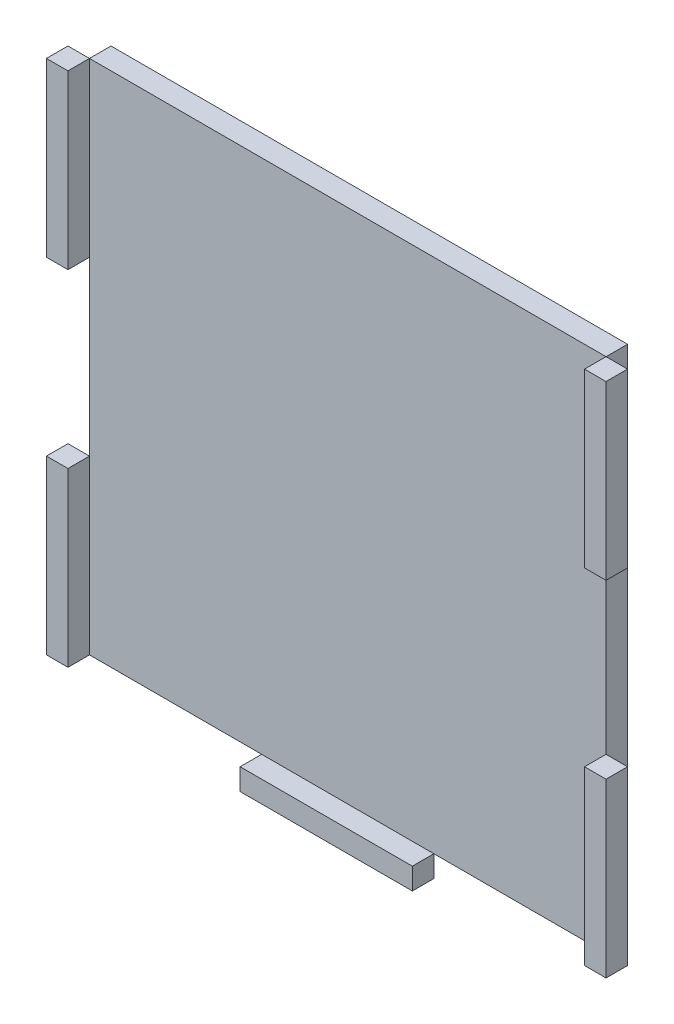
SolidWorks part; units mm, degrees
ref_plane "Front Plane" through (0, 0, 0) normal (0, 0, 1) x (1, 0, 0)
ref_plane "Top Plane" through (0, 0, 0) normal (0, 1, 0) x (1, 0, 0)
ref_plane "Right Plane" through (0, 0, 0) normal (1, 0, 0) x (0, 0, -1)
sketch "Sketch2" plane through (0, 0, 0) normal (0, 0, 1) x (1, 0, 0)
  line L1 (-38.1, -38.1) -> (38.1, -38.1)
  line L2 (-38.1, -38.1) -> (-38.1, 38.1)
  line L3 (-38.1, 38.1) -> (38.1, 38.1)
  line L4 (38.1, -38.1) -> (38.1, 38.1)
  line L5 (-38.1, -38.1) -> (38.1, 38.1) construction
  line L6 (-38.1, 38.1) -> (38.1, -38.1) construction
  point P0 (0, 0)
  dimension "D1" = 76.2
  dimension "D2" = 76.2
extrude "Boss-Extrude1" add sketch "Sketch2" along normal blind 3.175
sketch "Sketch4" plane through (0, 0, 3.175) normal (0, 0, 1) x (1, 0, 0)
  line L0 (-38.1, -38.1) -> (38.1, -38.1) construction
  line L1 (-38.1, 38.1) -> (-41.275, 38.1)
  line L2 (-38.1, 38.1) -> (-38.1, 12.7)
  line L3 (-38.1, 12.7) -> (-41.275, 12.7)
  line L4 (-41.275, 38.1) -> (-41.275, 12.7)
  line L5 (-38.1, -38.1) -> (-41.275, -38.1)
  line L6 (-38.1, -38.1) -> (-38.1, -12.7)
  line L7 (-38.1, -12.7) -> (-41.275, -12.7)
  line L8 (-41.275, -38.1) -> (-41.275, -12.7)
  line L9 (-12.7, -38.1) -> (12.7, -38.1)
  line L10 (-12.7, -38.1) -> (-12.7, -41.275)
  line L11 (-12.7, -41.275) -> (12.7, -41.275)
  line L12 (12.7, -38.1) -> (12.7, -41.275)
  line L14 (38.1, 38.1) -> (41.275, 38.1)
  line L15 (38.1, 38.1) -> (38.1, 12.7)
  line L16 (38.1, 12.7) -> (41.275, 12.7)
  line L17 (41.275, 38.1) -> (41.275, 12.7)
  line L18 (38.1, -38.1) -> (41.275, -38.1)
  line L19 (38.1, -38.1) -> (38.1, -12.7)
  line L20 (38.1, -12.7) -> (41.275, -12.7)
  line L21 (41.275, -38.1) -> (41.275, -12.7)
  dimension "D1" = 25.4
  dimension "D2" = 25.4
  dimension "D3" = 25.4
  dimension "D4" = 25.4
  dimension "D5" = 25.4
  dimension "D6" = 25.4
  dimension "D7" = 3.175
  dimension "D8" = 3.175
  dimension "D9" = 3.175
  dimension "D10" = 3.175
  dimension "D11" = 3.175
extrude "Boss-Extrude2" add sketch "Sketch4" along normal blind 3.175 separate body
